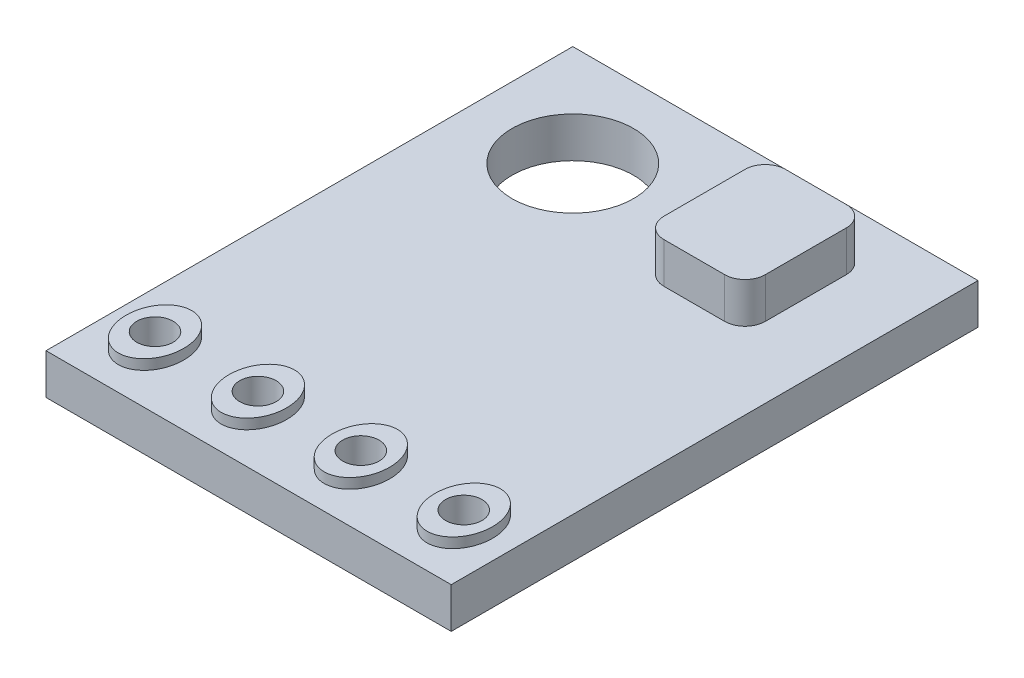
SolidWorks part; units mm, degrees
ref_plane "Front Plane" through (0, 0, 0) normal (0, 0, 1) x (1, 0, 0)
ref_plane "Top Plane" through (0, 0, 0) normal (0, 1, 0) x (1, 0, 0)
ref_plane "Right Plane" through (0, 0, 0) normal (1, 0, 0) x (0, 0, -1)
sketch "Sketch1" plane through (0, 0, 0) normal (0, 1, 0) x (1, 0, 0)
  line L1 (-5, 6.5) -> (5, 6.5)
  line L2 (-5, 6.5) -> (-5, -6.5)
  line L3 (-5, -6.5) -> (5, -6.5)
  line L4 (5, 6.5) -> (5, -6.5)
  line L5 (-5, 6.5) -> (5, -6.5) construction
  line L6 (-5, -6.5) -> (5, 6.5) construction
  circle A0 centre (-2.5, 4) radius 1.5
  point P0 (0, 0)
  dimension "D3" = 3
  dimension "D1" = 10
  dimension "D2" = 13
  dimension "D4" = 2.5
  dimension "D5" = 2.5
extrude "Boss-Extrude1" add sketch "Sketch1" along normal blind 1
sketch "Sketch2" plane through (0, 0, 0) normal (0, 1, 0) x (1, 0, 0)
  line L0 (5, 6.5) -> (-5, 6.5) construction
  line L1 (1.25, 5.5) -> (2.75, 5.5)
  line L2 (0.75, 5) -> (0.75, 3)
  line L3 (1.25, 2.5) -> (2.75, 2.5)
  line L4 (3.25, 5) -> (3.25, 3)
  line L5 (0.75, 5.5) -> (3.25, 2.5) construction
  line L6 (0.75, 2.5) -> (3.25, 5.5) construction
  line L7 (-5, 6.5) -> (-5, -6.5) construction
  arc A0 (1.25, 2.5) -> (0.75, 3) centre (1.25, 3) cw
  arc A1 (2.75, 2.5) -> (3.25, 3) centre (2.75, 3) ccw
  arc A2 (3.25, 5) -> (2.75, 5.5) centre (2.75, 5) ccw
  arc A3 (0.75, 5) -> (1.25, 5.5) centre (1.25, 5) cw
  point P0 (2, 4)
  dimension "D5" = 0.5
  dimension "D1" = 2.5
  dimension "D2" = 3
  dimension "D3" = 2.5
  dimension "D4" = 7
extrude "Boss-Extrude2" add sketch "Sketch2" along normal blind 2
sketch "Sketch3" plane through (0, 0, 0) normal (0, 1, 0) x (1, 0, 0)
  line L0 (0, 7.7954) -> (0, -7.7954) construction
  line L1 (-5, -6.5) -> (5, -6.5) construction
  circle A0 centre (-1.27, -5) radius 0.45
  circle A2 centre (-3.81, -5) radius 0.45
  circle A3 centre (3.81, -5) radius 0.45
  circle A4 centre (1.27, -5) radius 0.45
  ellipse E0 centre (-1.27, -5) end of major axis (-1.27, -5.9059) minor radius 0.7107
  ellipse E1 centre (-3.81, -5) end of major axis (-3.81, -5.9059) minor radius 0.7107
  ellipse E2 centre (3.81, -5) end of major axis (3.81, -5.9059) minor radius 0.7107
  ellipse E3 centre (1.27, -5) end of major axis (1.27, -5.9059) minor radius 0.7107
  point P4 (0, 0)
  dimension "D1" = 0.9
  dimension "D2" = 0.9
  dimension "D3" = 1.5
  dimension "D4" = 1.5
  dimension "D5" = 2.54
  dimension "D6" = 1.27
extrude "Boss-Extrude3" add sketch "Sketch3" along normal blind 1.25
sketch "Sketch4" plane through (0, 0, 0) normal (0, 1, 0) x (1, 0, 0)
  circle A0 centre (-3.81, -5) radius 0.45
  circle A1 centre (-1.27, -5) radius 0.45
  circle A2 centre (1.27, -5) radius 0.45
  circle A3 centre (3.81, -5) radius 0.45
extrude "Cut-Extrude1" cut sketch "Sketch4" against normal blind 2 and the other way through all
